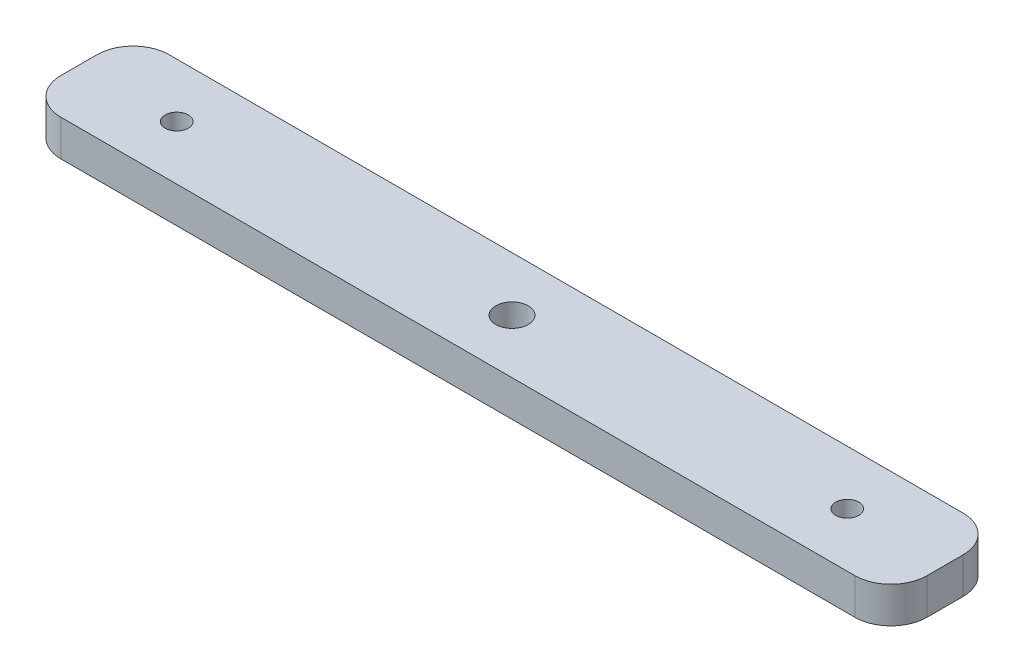
SolidWorks part; units mm, degrees
material "PBT Общее назначение"
ref_plane "Спереди" through (0, 0, 0) normal (0, 0, 1) x (1, 0, 0)
ref_plane "Сверху" through (0, 0, 0) normal (0, 1, 0) x (1, 0, 0)
ref_plane "Справа" through (0, 0, 0) normal (1, 0, 0) x (0, 0, -1)
sketch "Эскиз1" plane through (0, 0, 0) normal (0, 1, 0) x (1, 0, 0)
  line L0 (0, 0) -> (120, 0)
  line L1 (0, 0) -> (0, 15)
  line L2 (120, 0) -> (120, 15)
  line L3 (0, 15) -> (120, 15)
  dimension "D1" = 15
  dimension "D2" = 120
extrude "Бобышка-Вытянуть1" add sketch "Эскиз1" along normal blind 5
sketch "Эскиз2" plane through (0, 5, 0) normal (0, 1, 0) x (1, 0, 0)
  line L0 (60, 15) -> (60, 0) construction
  line L3 (120, 15) -> (0, 15) construction
  line L6 (0, 0) -> (120, 0) construction
  line L7 (13.55, 7.5) -> (106.45, 7.5) construction
  circle A0 centre (13.55, 7.5) radius 1.6
  circle A1 centre (106.45, 7.5) radius 1.6
  circle A2 centre (60, 7.5) radius 2.25
  point P8 (60, 7.5)
  point P9 (60, 7.5)
  dimension "D1" = 92.9
  dimension "D2" = 3.2
  dimension "D3" = 3.2
  dimension "D4" = 4.5
extrude "Вырез-Вытянуть1" cut sketch "Эскиз2" against normal through all
fillet "Скругление1" radius 5 4 edges at (0, 2.5, -15) (0, 2.5, 0) (120, 2.5, -15) (120, 2.5, 0)
